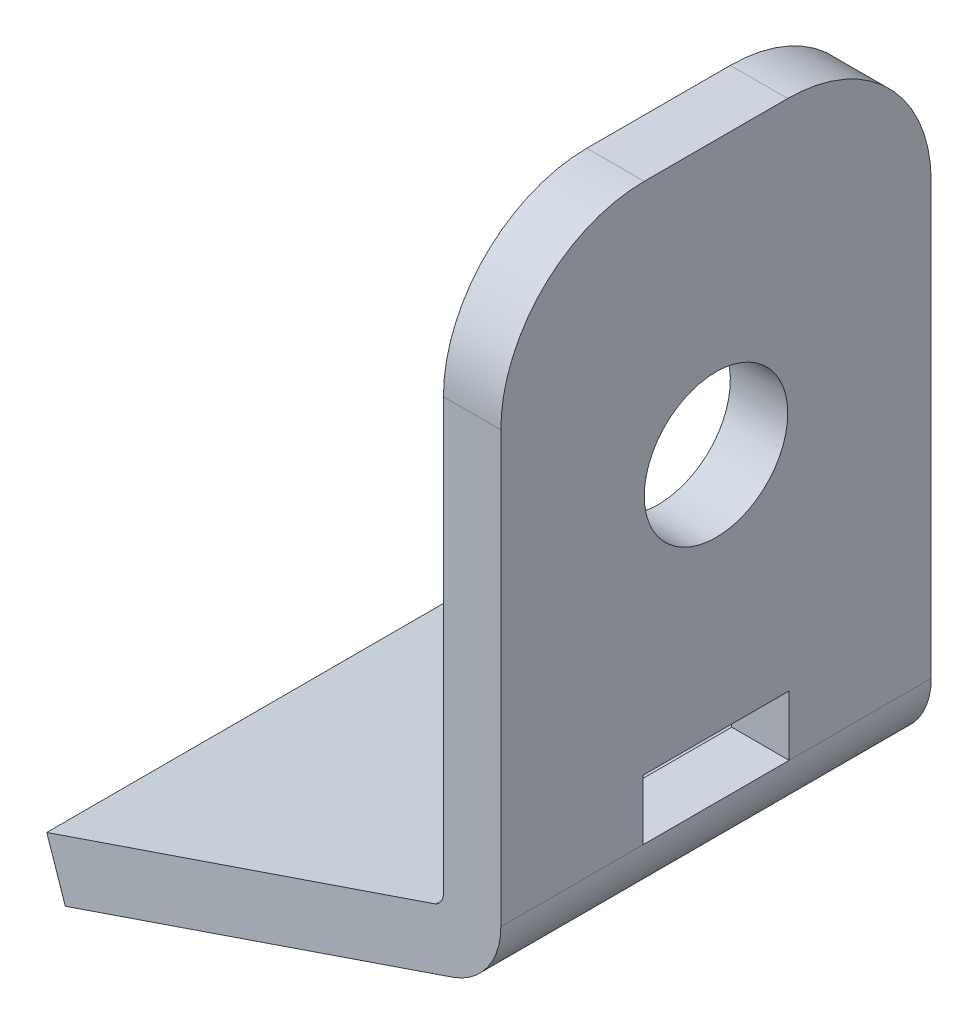
SolidWorks part; units mm, degrees
material "Stal węglowa"
ref_plane "Płaszczyzna przednia" through (0, 0, 0) normal (0, 0, 1) x (1, 0, 0)
ref_plane "Płaszczyzna górna" through (0, 0, 0) normal (0, 1, 0) x (1, 0, 0)
ref_plane "Płaszczyzna prawa" through (0, 0, 0) normal (1, 0, 0) x (0, 0, -1)
sketch "Szkic1" plane through (0, 0, 0) normal (0, 0, 1) x (1, 0, 0)
  line L0 (-21.455, -379.5774) -> (-23.8241, -380.3845)
  line L1 (-23.8241, -380.3845) -> (-23.1754, -382.2886)
  line L2 (-8, -355.3201) -> (-10, -355.3201) construction
  line L4 (-9.6427, -377.6693) -> (-23.1754, -382.2886)
  line L10 (-10.2887, -375.7733) -> (-21.455, -379.5774) construction
  line L16 (-8, -355.3201) -> (-10, -355.3201)
  line L24 (-10.2887, -375.7733) -> (-21.455, -379.5774)
  line L28 (-7.9978, -375.3201) -> (-8, -355.3201)
  line L29 (-10, -375.3201) -> (-10, -355.3201)
  arc A0 (-9.6427, -377.6693) -> (-7.9978, -375.3201) centre (-10.4978, -375.3201) ccw construction
  arc A1 (-10.2887, -375.7733) -> (-10, -375.3201) centre (-10.5, -375.3201) ccw construction
  arc A2 (-9.6427, -377.6693) -> (-7.9978, -375.3201) centre (-10.4978, -375.3201) ccw
  arc A3 (-10.2887, -375.7733) -> (-10, -375.3201) centre (-10.5, -375.3201) ccw
extrude "Dodanie-wyciągnięcie1" add sketch "Szkic1" against normal blind 15 contours A2 L28 L16 L29 A3 L24 L0 L1 L4
sketch "Szkic2" plane through (-10, 0, 0) normal (-1, 0, 0) x (0, 0, 1)
  circle A0 centre (-7.5, -364.8201) radius 2.5
extrude "Wytnij-wyciągnięcie2" cut sketch "Szkic2" against normal blind 15 contours A0
sketch "Szkic4" plane through (-10, 0, 0) normal (-1, 0, 0) x (0, 0, 1)
  line L2 (-15, -375.3201) -> (0, -375.3201) construction
  line L8 (-10.0482, -375.3201) -> (-4.9528, -375.3201)
  line L9 (-10.0482, -375.3201) -> (-10.0482, -373.2235)
  line L10 (-10.0482, -373.2235) -> (-4.9528, -373.2235)
  line L11 (-4.9528, -375.3201) -> (-4.9528, -373.2235)
extrude "Wytnij-wyciągnięcie4" cut sketch "Szkic4" against normal blind 15 contours L11 L10 L9 L8
fillet "Zaokrąglenie1" radius 5 2 edges at (-9, -355.3201, 0) (-9, -355.3201, -15)
